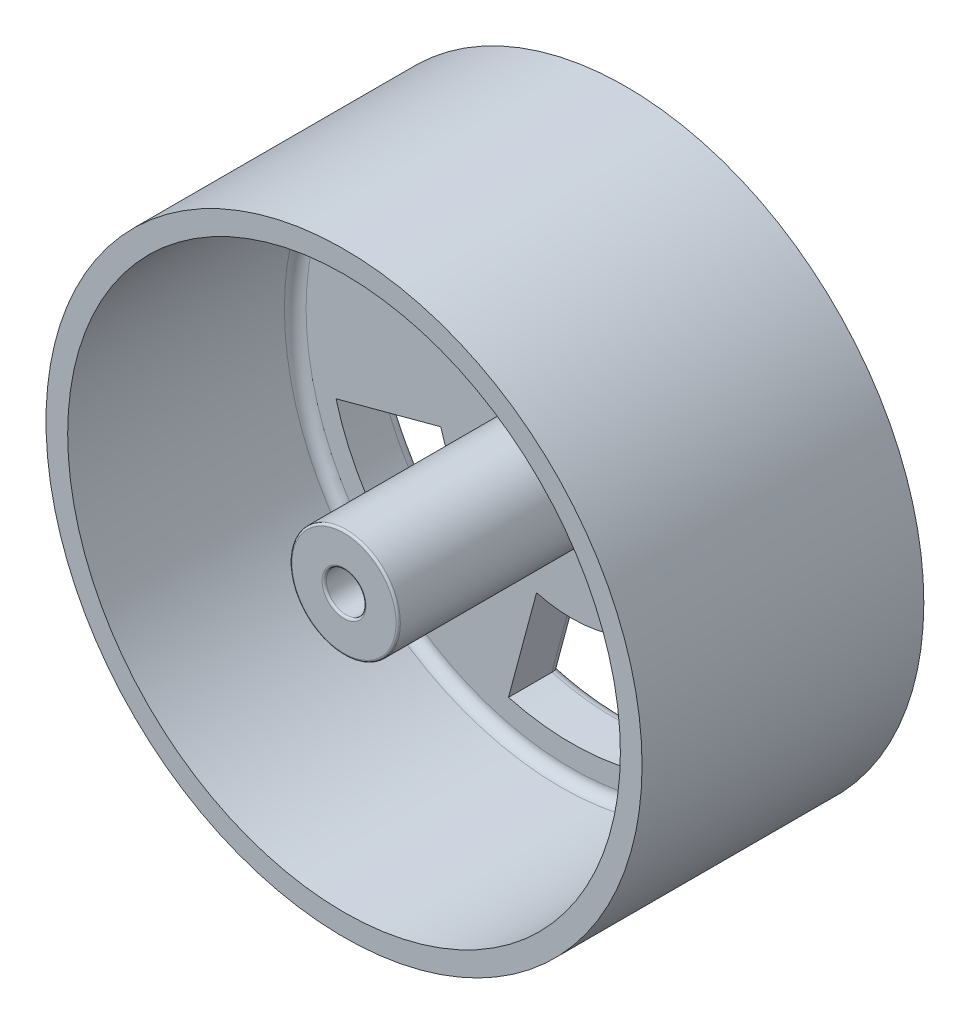
SolidWorks part; units mm, degrees
material "ABS"
ref_plane "Front Plane" through (0, 0, 0) normal (0, 0, 1) x (1, 0, 0)
ref_plane "Top Plane" through (0, 0, 0) normal (0, 1, 0) x (1, 0, 0)
ref_plane "Right Plane" through (0, 0, 0) normal (1, 0, 0) x (0, 0, -1)
sketch "Sketch1" plane through (0, 0, 0) normal (0, 0, 1) x (1, 0, 0)
  line L0 (0, 0) -> (-5.8234, 21.7333) construction
  line L1 (0, 0) -> (5.8234, 21.7333) construction
  line L2 (-5.8234, 21.7333) -> (-3.2352, 12.0741)
  line L3 (5.8234, 21.7333) -> (3.2352, 12.0741)
  line L4 (15.9099, 15.9099) -> (8.8388, 8.8388)
  line L5 (21.7333, 5.8234) -> (12.0741, 3.2352)
  line L6 (21.7333, -5.8234) -> (12.0741, -3.2352)
  line L7 (15.9099, -15.9099) -> (8.8388, -8.8388)
  line L8 (5.8234, -21.7333) -> (3.2352, -12.0741)
  line L9 (-5.8234, -21.7333) -> (-3.2352, -12.0741)
  line L10 (-15.9099, -15.9099) -> (-8.8388, -8.8388)
  line L11 (-21.7333, -5.8234) -> (-12.0741, -3.2352)
  line L12 (-21.7333, 5.8234) -> (-12.0741, 3.2352)
  line L13 (-15.9099, 15.9099) -> (-8.8388, 8.8388)
  circle A0 centre (0, 0) radius 27.5
  arc A1 (-5.8234, 21.7333) -> (5.8234, 21.7333) centre (0, 0) cw
  arc A2 (-3.2352, 12.0741) -> (3.2352, 12.0741) centre (0, 0) cw
  arc A3 (15.9099, 15.9099) -> (21.7333, 5.8234) centre (0, 0) cw
  arc A4 (8.8388, 8.8388) -> (12.0741, 3.2352) centre (0, 0) cw
  arc A5 (21.7333, -5.8234) -> (15.9099, -15.9099) centre (0, 0) cw
  arc A6 (12.0741, -3.2352) -> (8.8388, -8.8388) centre (0, 0) cw
  arc A7 (5.8234, -21.7333) -> (-5.8234, -21.7333) centre (0, 0) cw
  arc A8 (3.2352, -12.0741) -> (-3.2352, -12.0741) centre (0, 0) cw
  arc A9 (-15.9099, -15.9099) -> (-21.7333, -5.8234) centre (0, 0) cw
  arc A10 (-8.8388, -8.8388) -> (-12.0741, -3.2352) centre (0, 0) cw
  arc A11 (-21.7333, 5.8234) -> (-15.9099, 15.9099) centre (0, 0) cw
  arc A12 (-12.0741, 3.2352) -> (-8.8388, 8.8388) centre (0, 0) cw
  point P5 (0, 22.5)
  point P31 (0, 0)
  dimension "D1" = 55
  dimension "D3" = 5
  dimension "D2" = 30
  dimension "D4" = 10
  dimension "D5" = 6
extrude "Boss-Extrude1" add sketch "Sketch1" along normal blind 5
sketch "Sketch2" plane through (0, 0, 0) normal (0, 0, 1) x (1, 0, 0)
  circle A0 centre (0, 0) radius 27.5 construction
  circle A1 centre (0, 0) radius 27.5
  circle A2 centre (0, 0) radius 25.5
  circle A3 centre (0, 0) radius 5
  dimension "D2" = 10
  dimension "D1" = 2
extrude "Boss-Extrude3" add sketch "Sketch2" along normal blind 26 contours A1 | A2 | A3
sketch "Sketch3" plane through (0, 0, 26) normal (0, 0, 1) x (1, 0, 0)
  circle A0 centre (0, 0) radius 1.83
  dimension "D1" = 3.66
extrude "Cut-Extrude1" cut sketch "Sketch3" against normal blind 5.3
fillet "Fillet1" radius 1 2 edges at (5, 0, 5) (25.5, 0, 5)
fillet "Fillet2" radius 1 28 edges at (0, 12.5, 5) (4.5293, 16.9037, 5) (0, 22.5, 5) (-4.5293, 16.9037, 5) (10.8253, 6.25, 0) (12.3744, 12.3744, 0) (19.4856, 11.25, 0) (16.9037, 4.5293, 0) (10.8253, -6.25, 0) (16.9037, -4.5293, 0) (12.3744, -12.3744, 0) (19.4856, -11.25, 0) (0, -22.5, 0) (4.5293, -16.9037, 0) (-4.5293, -16.9037, 0) (0, -12.5, 0) (-19.4856, -11.25, 0) (-12.3744, -12.3744, 0) (-10.8253, -6.25, 0) (-16.9037, -4.5293, 0) (-19.4856, 11.25, 0) (-16.9037, 4.5293, 0) (-10.8253, 6.25, 0) (-12.3744, 12.3744, 0) (-4.5293, 16.9037, 0) (0, 22.5, 0) (4.5293, 16.9037, 0) (0, 12.5, 0)
sketch "Sketch4" plane through (0, 0, 0) normal (0, 0, -1) x (-1, 0, 0)
  circle A0 centre (0, 0) radius 4
  dimension "D1" = 8
extrude "Cut-Extrude2" cut sketch "Sketch4" against normal blind 1
fillet "Fillet3" radius 0.2 3 edges at (1.83, 0, 20.7) (1.83, 0, 26) (5, 0, 26)
